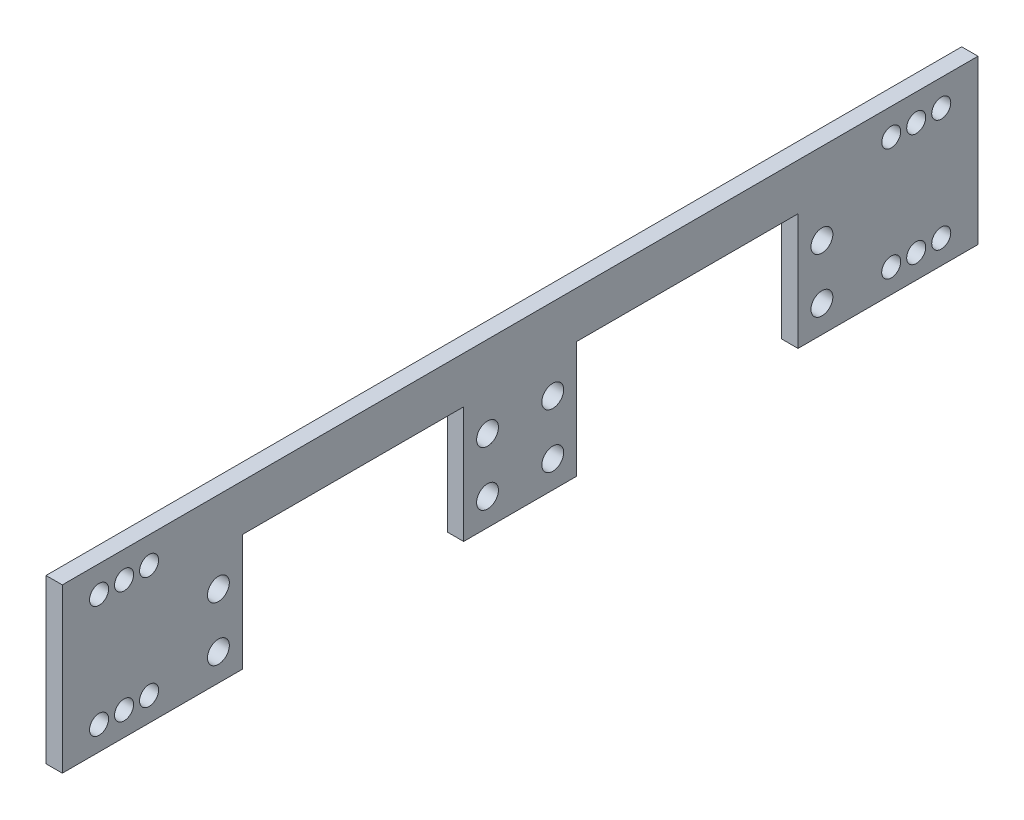
SolidWorks part; units mm, degrees
ref_plane "Front Plane" through (0, 0, 0) normal (0, 0, 1) x (1, 0, 0)
ref_plane "Top Plane" through (0, 0, 0) normal (0, 1, 0) x (1, 0, 0)
ref_plane "Right Plane" through (0, 0, 0) normal (1, 0, 0) x (0, 0, -1)
sketch "Sketch1" plane through (0, 0, 0) normal (1, 0, 0) x (0, 0, -1)
  line L0 (-51.1065, 0) -> (-51.1065, 21.4565)
  line L1 (-84.21, 0) -> (-77.45, 4.4083)
  line L2 (-84.21, 0) -> (-51.1065, 0)
  line L3 (-84.21, 0) -> (-84.21, 30)
  line L4 (-84.21, 30) -> (84.21, 30)
  line L5 (84.21, 0) -> (84.21, 30)
  line L6 (-51.1065, 21.4565) -> (-10.3935, 21.4565)
  line L7 (-10.3935, 0) -> (-10.3935, 21.4565)
  line L8 (-10.3935, 0) -> (10.3935, 0)
  line L9 (10.3935, 0) -> (10.3935, 21.4565)
  line L10 (51.1065, 0) -> (51.1065, 21.4565)
  line L11 (10.3935, 21.4565) -> (51.1065, 21.4565)
  line L12 (51.1065, 0) -> (84.21, 0)
  line L13 (-77.45, 4.4083) -> (-72.85, 4.4083)
  line L14 (-72.85, 4.4083) -> (-68.25, 4.4083)
  line L15 (-68.25, 4.4083) -> (-77.45, 25.1117)
  line L16 (-77.45, 25.1117) -> (-72.85, 25.1117)
  line L17 (-72.85, 25.1117) -> (-68.25, 25.1117)
  line L18 (-68.25, 25.1117) -> (-55.5, 15)
  line L19 (-55.5, 15) -> (-55.5, 5)
  line L20 (-55.5, 5) -> (-6, 5)
  line L21 (-6, 5) -> (-6, 15)
  line L22 (-6, 15) -> (6, 5)
  line L23 (6, 5) -> (6, 15)
  line L24 (6, 15) -> (55.5, 15)
  line L25 (55.5, 15) -> (55.5, 5)
  line L26 (55.5, 5) -> (68.25, 25.1117)
  line L27 (68.25, 25.1117) -> (68.25, 4.4083)
  line L28 (68.25, 4.4083) -> (72.85, 25.1117)
  line L29 (72.85, 25.1117) -> (72.85, 4.4083)
  line L30 (72.85, 4.4083) -> (76.9354, 4.4083)
  line L31 (76.9354, 4.4083) -> (77.45, 4.4083)
  line L32 (77.45, 4.4083) -> (77.45, 25.1117)
  line L33 (77.45, 25.1117) -> (30.75, 15)
  circle A0 centre (-72.85, 25.1117) radius 1.75
  circle A1 centre (-68.25, 25.1117) radius 1.75
  circle A2 centre (-77.45, 25.1117) radius 1.75
  circle A3 centre (-72.85, 4.4083) radius 1.75
  circle A4 centre (-68.25, 4.4083) radius 1.75
  circle A5 centre (-77.45, 4.4083) radius 1.75
  circle A8 centre (68.25, 4.4083) radius 1.75
  circle A9 centre (72.85, 4.4083) radius 1.75
  circle A10 centre (77.45, 4.4083) radius 1.75
  circle A11 centre (77.45, 25.1117) radius 1.75
  circle A12 centre (72.85, 25.1117) radius 1.75
  circle A13 centre (68.25, 25.1117) radius 1.7397
  circle A14 centre (-55.5, 15) radius 2.01
  circle A15 centre (-55.5, 5) radius 2.01
  circle A16 centre (-6, 5) radius 2.01
  circle A17 centre (-6, 15) radius 2.01
  circle A18 centre (6, 15) radius 2.01
  circle A19 centre (6, 5) radius 2.01
  circle A20 centre (55.5, 15) radius 2.01
  circle A21 centre (55.5, 5) radius 2.01
extrude "Boss-Extrude1" add sketch "Sketch1" along normal blind 3 contours A21 L25 A20 L24 L10 L12 L5 L4 L3 L1 A5 L13 A3 L14 A4 L15 A2 L16 A0 L17 A1 L18 A14 L19 A15 L20 L0 L6 L7 A16 L21 A17 L22 A19 L23 A18 L9 L11 L33 L26 A13 L27 A12 A11 L32 A10 | A15 L19 A14 L18 A1 L17 A0 L16 A2 L15 A4 L14 A3 L13 A5 L1 L2 L0 L20 | A19 L22 A17 L21 A16 L20 L7 L8 L9 L24 A18 L23 | A21 L26 L33 L10 L24 A20 L25 | A12 L29 A9 L30 A10 L32 A11 L33 | A12 L33 L27 A8 L28
sketch "Sketch2" plane through (0, 0, 0) normal (-1, 0, 0) x (0, 0, 1)
  line L0 (-68.25, 23.372) -> (-68.25, 23.1196)
  line L1 (-68.25, 23.1196) -> (-66.8257, 22.8113)
  line L2 (-68.25, 23.1196) -> (-66.7862, 22.8027) construction
  line L3 (-66.7862, 22.8027) -> (-67.3185, 23.6424)
  line L4 (-66.8257, 22.8113) -> (-66.7862, 22.8027)
  arc A0 (-68.25, 23.372) -> (-67.3185, 23.6424) centre (-68.25, 25.1117) ccw
extrude "Boss-Extrude2" add sketch "Sketch2" against normal blind 3
